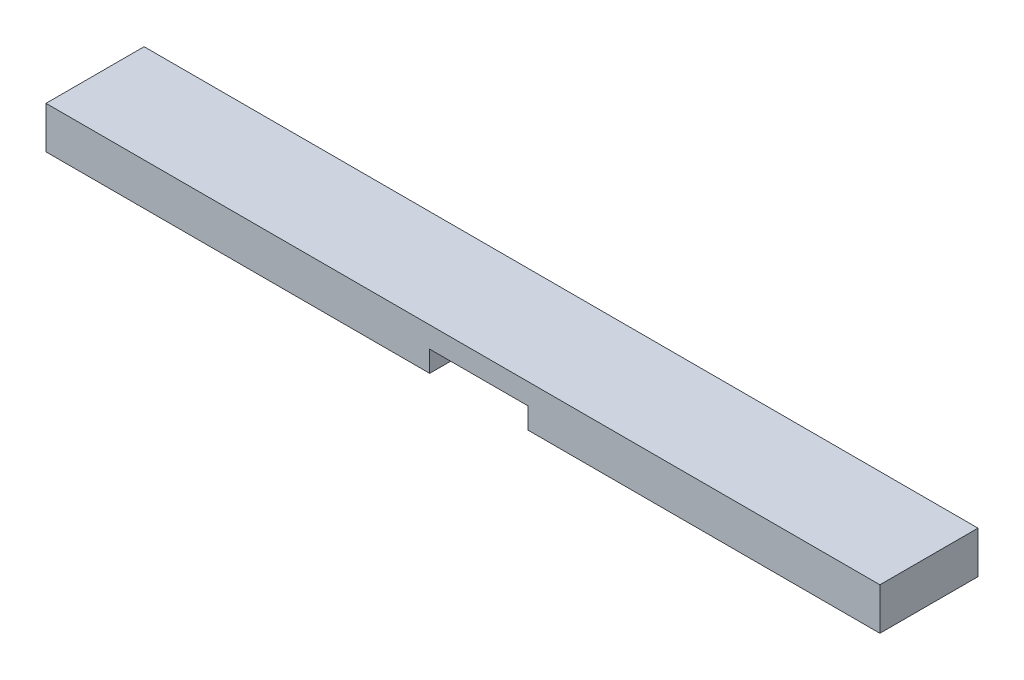
SolidWorks part; units mm, degrees
material "Pine"
ref_plane "Front Plane" through (0, 0, 0) normal (0, 0, 1) x (1, 0, 0)
ref_plane "Top Plane" through (0, 0, 0) normal (0, 1, 0) x (1, 0, 0)
ref_plane "Right Plane" through (0, 0, 0) normal (1, 0, 0) x (0, 0, -1)
sketch "Sketch1" plane through (0, 0, 0) normal (0, 1, 0) x (1, 0, 0)
  line L1 (0, 0) -> (755.65, 0)
  line L2 (0, 0) -> (0, 88.9)
  line L3 (0, 88.9) -> (755.65, 88.9)
  line L4 (755.65, 0) -> (755.65, 88.9)
  dimension "D1" = 88.9
  dimension "D2" = 755.65
extrude "Boss-Extrude1" add sketch "Sketch1" along normal blind 38.1
sketch "Sketch2" plane through (0, 0, 0) normal (0, -1, 0) x (1, 0, 0)
  line L0 (0, 0) -> (755.65, 0) construction
  line L1 (347.6752, 0) -> (436.5752, 0)
  line L2 (347.6752, 0) -> (347.6752, -88.9)
  line L3 (347.6752, -88.9) -> (436.5752, -88.9)
  line L4 (436.5752, 0) -> (436.5752, -88.9)
  line L5 (755.65, -88.9) -> (0, -88.9) construction
  dimension "D1" = 347.6752
  dimension "D2" = 88.9
extrude "Cut-Extrude1" cut sketch "Sketch2" against normal blind 19.05
